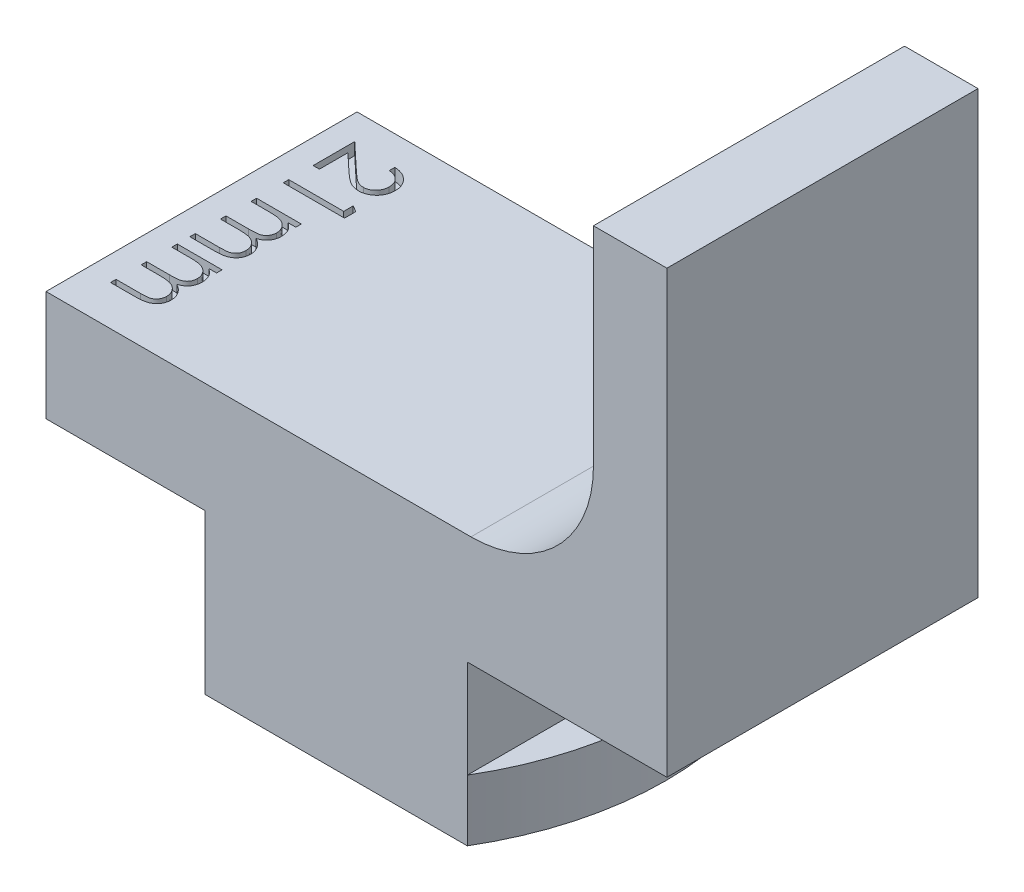
SolidWorks part; units mm, degrees
ref_plane "Front Plane" through (0, 0, 0) normal (0, 0, 1) x (1, 0, 0)
ref_plane "Top Plane" through (0, 0, 0) normal (0, 1, 0) x (1, 0, 0)
ref_plane "Right Plane" through (0, 0, 0) normal (1, 0, 0) x (0, 0, -1)
sketch "Sketch1" plane through (0, 0, 0) normal (0, 0, 1) x (1, 0, 0)
  line L0 (0, 0) -> (0, -4)
  line L1 (0, -4) -> (-1.75, -4)
  line L2 (-1.75, -4) -> (-1.75, -6.5)
  line L8 (12.45, -6.5) -> (12.45, -4)
  line L9 (12.45, -4) -> (10.7, -4)
  line L10 (10.7, -4) -> (10.7, 0)
  line L11 (10.7, 0) -> (18.85, 0)
  line L12 (18.85, 0) -> (18.85, 18)
  line L13 (18.85, 18) -> (15.85, 18)
  line L14 (15.85, 18) -> (15.85, 4.5)
  line L15 (15.85, 4.5) -> (-6.5, 4.5)
  line L16 (-6.5, 4.5) -> (-6.5, 0)
  line L17 (-6.5, 0) -> (0, 0)
  line L18 (5.35, -6.5) -> (5.35, 15) construction
  line L19 (-1.75, -6.5) -> (12.45, -6.5)
  circle A0 centre (5.35, 15) radius 10.5 construction
  point P3 (5.35, -6.5)
  dimension "D9" = 15
  dimension "D8" = 21
  dimension "D2" = 2.5
  dimension "D3" = 10.7
  dimension "D4" = 4
  dimension "D5" = 14.2
  dimension "D6" = 3
  dimension "D7" = 3
  dimension "D10" = 6.5
extrude "Boss-Extrude1" add sketch "Sketch1" along normal blind 12.7
fillet "Fillet1" radius 5 1 edges at (15.85, 4.5, 6.35)
sketch "Sketch2" plane through (0, -4, 0) normal (0, 1, 0) x (1, 0, 0)
  line L0 (0, -12.7) -> (10.7, -12.7)
  line L1 (10.7, 0) -> (0, 0)
  line L2 (-1.75, -12.7) -> (-1.75, 0) construction
  line L3 (12.45, -12.7) -> (12.45, 0) construction
  arc A0 (10.7, 0) -> (10.7, -12.7) centre (0.0543, -6.35) cw
  arc A1 (0, 0) -> (0, -12.7) centre (10.6457, -6.35) ccw
extrude "Cut-Extrude1" cut sketch "Sketch2" against normal blind 10 flip side to cut
sketch "Sketch3" plane through (0, 4.5, 0) normal (0, 1, 0) x (1, 0, 0)
  line L0 (-5.5, -1) -> (-5.5, -12.0066) construction
  line L1 (-6.5, -12.7) -> (-6.5, 0) construction
  line L2 (10.85, 0) -> (-6.5, 0) construction
  text T0 "21mm" font "Century Gothic" height 2.5
  dimension "D1" = 1
  dimension "D2" = 1
extrude "Cut-Extrude2" cut sketch "Sketch3" against normal blind 0.5
